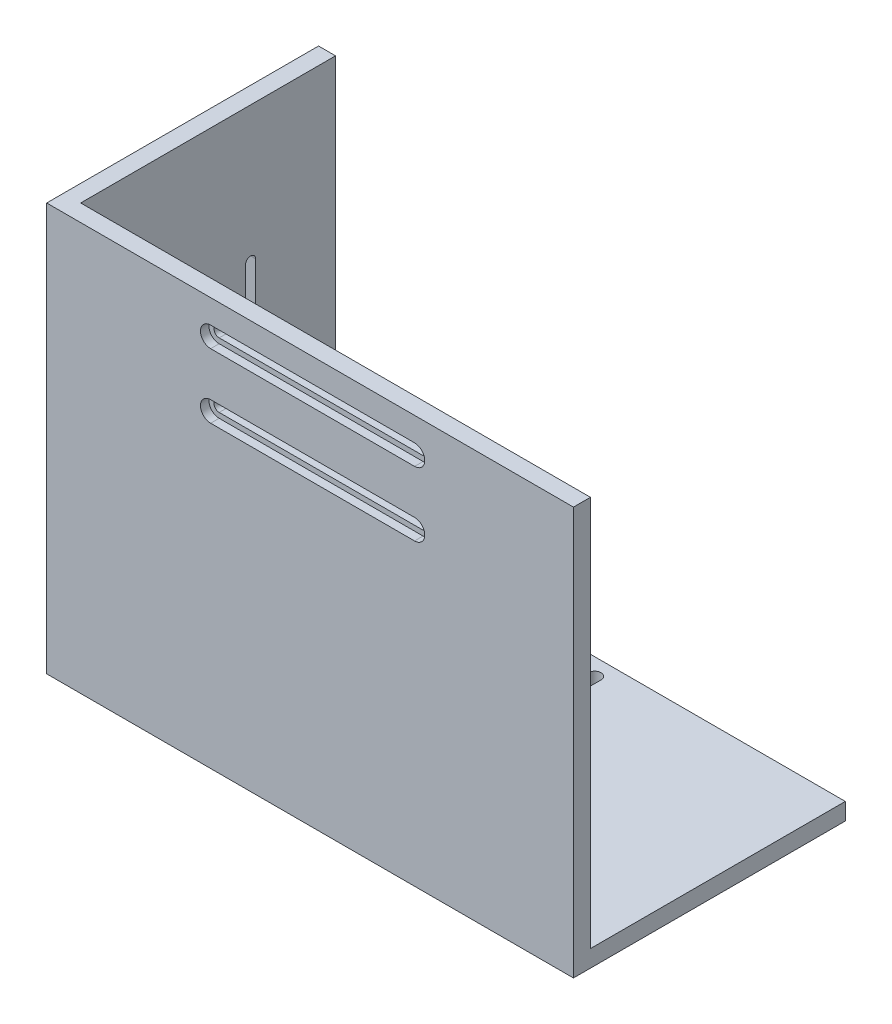
SolidWorks part; units mm, degrees
ref_plane "前视基准面" through (0, 0, 0) normal (0, 0, 1) x (1, 0, 0)
ref_plane "上视基准面" through (0, 0, 0) normal (0, 1, 0) x (1, 0, 0)
ref_plane "右视基准面" through (0, 0, 0) normal (1, 0, 0) x (0, 0, -1)
sketch "草图1" plane through (0, 0, 0) normal (0, 0, 1) x (1, 0, 0)
  line L1 (0, 0) -> (5, 0)
  line L2 (0, 0) -> (0, -120)
  line L3 (0, -120) -> (5, -120)
  line L4 (5, 0) -> (5, -120)
  dimension "D1" = 5
  dimension "D2" = 120
extrude "凸台-拉伸1" add sketch "草图1" along normal blind 80
sketch "草图2" plane through (5, 0, 0) normal (1, 0, 0) x (0, 0, -1)
  line L0 (0, -120) -> (0, 0) construction
  line L1 (-80, -120) -> (0, -120)
  line L2 (-80, -120) -> (-80, -115)
  line L3 (-80, -115) -> (0, -115)
  line L4 (0, -120) -> (0, -115)
  dimension "D1" = 5
extrude "凸台-拉伸2" add sketch "草图2" along normal blind 150
sketch "草图3" plane through (5, 0, 0) normal (1, 0, 0) x (0, 0, -1)
  line L0 (-40, 0) -> (-40, -72.5137) construction
  line L1 (-80, 0) -> (0, 0) construction
  line L2 (-25, -40) -> (-55, -40) construction
  line L3 (-55, -40) -> (-55, -80) construction
  line L4 (-53.5, -40) -> (-53.5, -80)
  line L5 (-56.5, -40) -> (-56.5, -80)
  line L6 (-25, -40) -> (-25, -80) construction
  line L7 (-26.5, -40) -> (-26.5, -80)
  line L8 (-23.5, -40) -> (-23.5, -80)
  line L9 (-62.5, -100) -> (-17.5, -100) construction
  line L10 (-62.5, -95) -> (-17.5, -95)
  line L11 (-62.5, -105) -> (-17.5, -105)
  line L12 (0, -115) -> (-80, -115) construction
  arc A0 (-53.5, -40) -> (-56.5, -40) centre (-55, -40) ccw
  arc A1 (-56.5, -80) -> (-53.5, -80) centre (-55, -80) ccw
  arc A2 (-26.5, -40) -> (-23.5, -40) centre (-25, -40) cw
  arc A3 (-23.5, -80) -> (-26.5, -80) centre (-25, -80) cw
  arc A4 (-62.5, -95) -> (-62.5, -105) centre (-62.5, -100) ccw
  arc A5 (-17.5, -105) -> (-17.5, -95) centre (-17.5, -100) ccw
  point P4 (-55, -60)
  point P7 (-40, -40)
  point P14 (-25, -60)
  point P21 (-40, -100)
  dimension "D2" = 1.5
  dimension "D6" = 5
  dimension "D1" = 30
  dimension "D3" = 40
  dimension "D4" = 20
  dimension "D5" = 15
  dimension "D7" = 45
extrude "切除-拉伸1" cut sketch "草图3" against normal up to next
sketch "草图4" plane through (5, 0, 0) normal (1, 0, 0) x (0, 0, -1)
  line L0 (0, -115) -> (-80, -115) construction
  line L1 (-80, 0) -> (-75, 0)
  line L2 (-80, 0) -> (-80, -115)
  line L3 (-80, -115) -> (-75, -115)
  line L4 (-75, 0) -> (-75, -115)
  dimension "D1" = 5
extrude "凸台-拉伸3" add sketch "草图4" along normal up to vertex (150 mm away) up to point (155, -115, 80)
sketch "草图6" plane through (0, 0, 75) normal (0, 0, -1) x (-1, 0, 0)
  line L0 (-48.25, -10) -> (-108.25, -10) construction
  line L1 (-48.25, -11.5) -> (-108.25, -11.5)
  line L2 (-48.25, -8.5) -> (-108.25, -8.5)
  line L3 (-155, 0) -> (-5, 0) construction
  line L6 (-81.6028, -19.5) -> (-35.0527, -19.5) construction
  line L7 (-48.25, -29) -> (-108.25, -29) construction
  line L8 (-48.25, -27.5) -> (-108.25, -27.5)
  line L9 (-48.25, -30.5) -> (-108.25, -30.5)
  line L10 (-5, -115) -> (-5, 0) construction
  arc A0 (-48.25, -11.5) -> (-48.25, -8.5) centre (-48.25, -10) ccw
  arc A1 (-108.25, -8.5) -> (-108.25, -11.5) centre (-108.25, -10) ccw
  arc A2 (-48.25, -27.5) -> (-48.25, -30.5) centre (-48.25, -29) cw
  arc A3 (-108.25, -30.5) -> (-108.25, -27.5) centre (-108.25, -29) cw
  point P2 (-78.25, -10)
  point P15 (-78.25, -29)
  dimension "D4" = 1.5
  dimension "D1" = 10
  dimension "D2" = 43.25
  dimension "D3" = 60
  dimension "D5" = 9.5
sketch "草图8" plane through (0, 0, 80) normal (0, 0, 1) x (1, 0, 0)
  line L0 (48.25, -10) -> (108.25, -10) construction
  line L1 (48.25, -7) -> (108.25, -7)
  line L2 (48.25, -13) -> (108.25, -13)
  line L3 (35.0527, -19.5) -> (81.6028, -19.5) construction
  line L4 (48.25, -29) -> (108.25, -29) construction
  line L5 (48.25, -32) -> (108.25, -32)
  line L6 (48.25, -26) -> (108.25, -26)
  arc A0 (48.25, -7) -> (48.25, -13) centre (48.25, -10) ccw
  arc A1 (108.25, -13) -> (108.25, -7) centre (108.25, -10) ccw
  arc A2 (48.25, -32) -> (48.25, -26) centre (48.25, -29) cw
  arc A3 (108.25, -26) -> (108.25, -32) centre (108.25, -29) cw
  point P4 (78.25, -10)
  point P15 (78.25, -29)
  dimension "D1" = 3
extrude "切除-拉伸4" cut sketch "草图8" against normal blind 2.5
extrude "切除-拉伸5" cut sketch "草图6" against normal through all
sketch "草图9" plane through (0, -115, 0) normal (0, 1, 0) x (1, 0, 0)
  line L0 (5, 0) -> (5, -75) construction
  line L2 (76.25, -10) -> (76.25, -59) construction
  line L3 (80.25, -10) -> (80.25, -59)
  line L4 (72.25, -10) -> (72.25, -59)
  line L5 (66.25, -5) -> (66.25, -65) construction
  line L6 (67.75, -5) -> (67.75, -65)
  line L7 (64.75, -5) -> (64.75, -65)
  line L8 (155, -75) -> (5, -75) construction
  line L9 (76.25, -10) -> (76.25, -59) construction
  line L10 (86.25, -5) -> (86.25, -65) construction
  line L11 (88.1099, -5) -> (88.1099, -65)
  line L12 (84.3901, -5) -> (84.3901, -65)
  line L13 (66.25, -5) -> (86.25, -5) construction
  line L14 (155, 0) -> (5, 0) construction
  circle A0 centre (76.25, -10) radius 4 construction
  arc A1 (80.25, -10) -> (72.25, -10) centre (76.25, -10) ccw
  arc A2 (72.25, -59) -> (80.25, -59) centre (76.25, -59) ccw
  arc A3 (67.75, -5) -> (64.75, -5) centre (66.25, -5) ccw
  arc A4 (64.75, -65) -> (67.75, -65) centre (66.25, -65) ccw
  arc A5 (88.1099, -5) -> (84.3901, -5) centre (86.25, -5) ccw
  arc A6 (84.3901, -65) -> (88.1099, -65) centre (86.25, -65) ccw
  point P6 (76.25, -34.5)
  point P14 (66.25, -35)
  point P25 (86.25, -35)
  point P32 (86.25, -65)
  dimension "D3" = 8
  dimension "D4" = 4
  dimension "D7" = 1.5
  dimension "D1" = 71.25
  dimension "D2" = 10
  dimension "D5" = 59
  dimension "D6" = 10
  dimension "D8" = 60
  dimension "D9" = 70
  dimension "D10" = 10
  dimension "D11" = 60
extrude "切除-拉伸6" cut sketch "草图9" against normal through all
